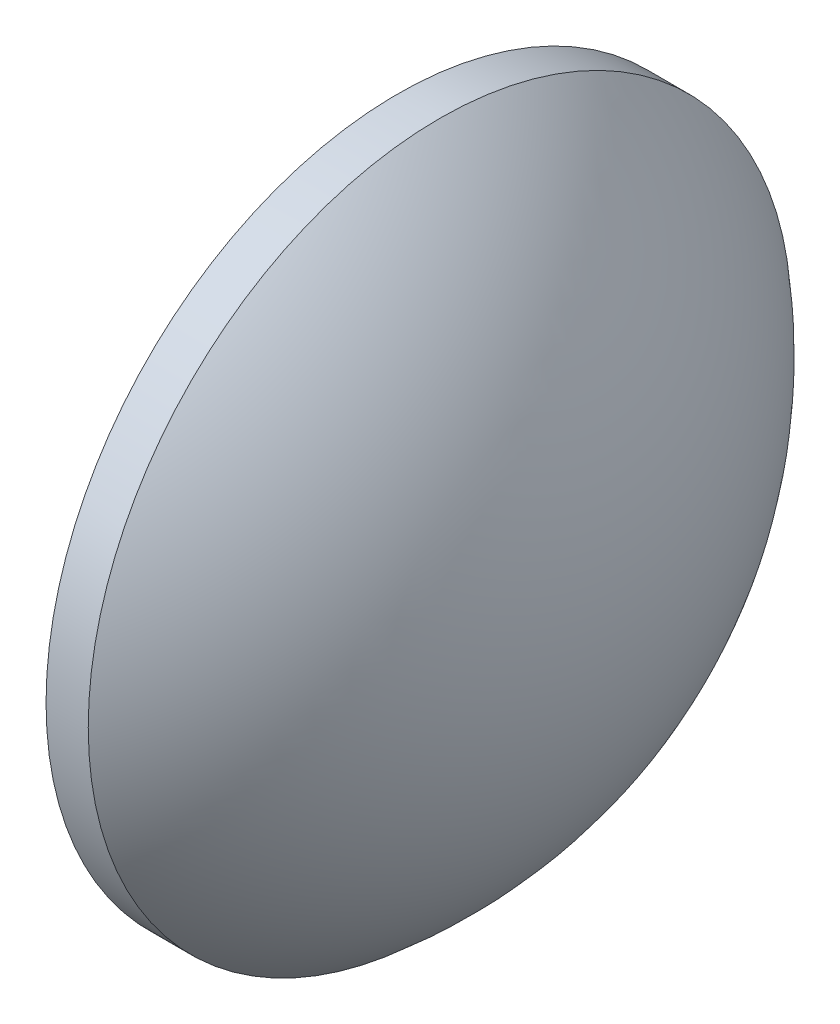
SolidWorks part; units mm, degrees
ref_plane "前视基准面" through (0, 0, 0) normal (0, 0, 1) x (1, 0, 0)
ref_plane "上视基准面" through (0, 0, 0) normal (0, 1, 0) x (1, 0, 0)
ref_plane "右视基准面" through (0, 0, 0) normal (1, 0, 0) x (0, 0, -1)
sketch "草图1" plane through (0, 0, 0) normal (0, 0, 1) x (1, 0, 0)
  line L0 (429.6882, 106.6708) -> (456.5797, 106.6708) construction
  line L1 (439.1104, 106.6708) -> (439.1104, 131.6708)
  line L2 (453.8404, 106.6708) -> (439.1104, 106.6708)
  line L5 (439.1104, 131.6708) -> (442.1104, 131.6708)
  arc A0 (453.8404, 106.6708) -> (442.1104, 131.6708) centre (421.3343, 106.6708) ccw
revolve "旋转1" add sketch "草图1" angle 360 about L0
